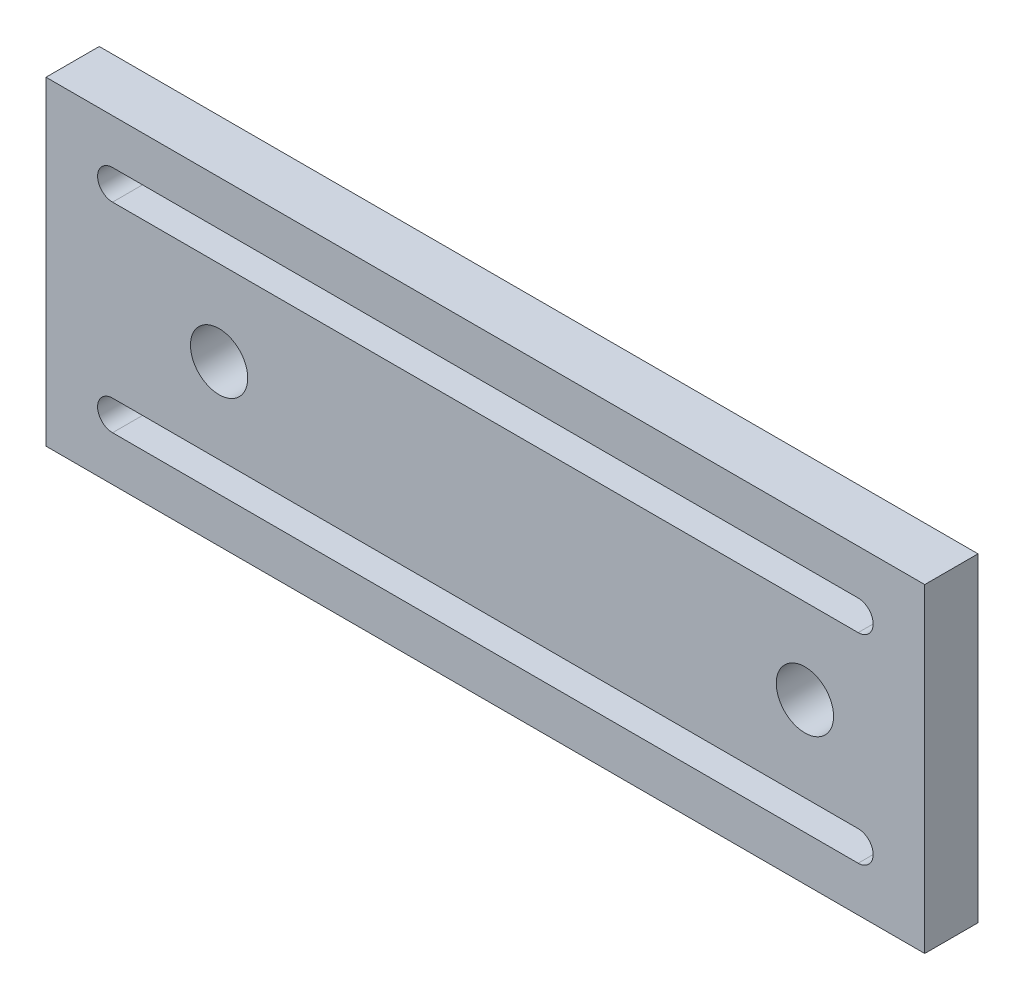
SolidWorks part; units mm, degrees
ref_plane "Front Plane" through (0, 0, 0) normal (0, 0, 1) x (1, 0, 0)
ref_plane "Top Plane" through (0, 0, 0) normal (0, 1, 0) x (1, 0, 0)
ref_plane "Right Plane" through (0, 0, 0) normal (1, 0, 0) x (0, 0, -1)
sketch "Sketch1" plane through (0, 0, 0) normal (0, 0, 1) x (1, 0, 0)
  line L0 (-56, -15) -> (56, -15) construction
  line L1 (66, -24) -> (-66, -24)
  line L2 (66, -24) -> (66, 24)
  line L3 (66, 24) -> (-66, 24)
  line L4 (-66, -24) -> (-66, 24)
  line L5 (66, -24) -> (-66, 24) construction
  line L6 (66, 24) -> (-66, -24) construction
  line L7 (56, 12.75) -> (-56, 12.75)
  line L8 (-56, -12.75) -> (56, -12.75)
  line L9 (56, 17.25) -> (-56, 17.25)
  line L10 (-56, -17.25) -> (56, -17.25)
  arc A0 (-56, 17.25) -> (-56, 12.75) centre (-56, 15) ccw
  arc A1 (56, 12.75) -> (56, 17.25) centre (56, 15) ccw
  circle A2 centre (-40, 0) radius 4.3033
  circle A3 centre (48, 0) radius 4.3033
  arc A4 (-56, -12.75) -> (-56, -17.25) centre (-56, -15) ccw
  arc A5 (56, -17.25) -> (56, -12.75) centre (56, -15) ccw
  point P0 (0, 0)
  point P6 (0, 15)
  point P19 (0, -15)
  dimension "D1" = 132
  dimension "D2" = 48
  dimension "D3" = 112
  dimension "D4" = 24
  dimension "D5" = 106
  dimension "D6" = 4.5
  dimension "D7" = 18
  dimension "D8" = 4.5
  dimension "D9" = 9
extrude "Boss-Extrude1" add sketch "Sketch1" along normal blind 8
